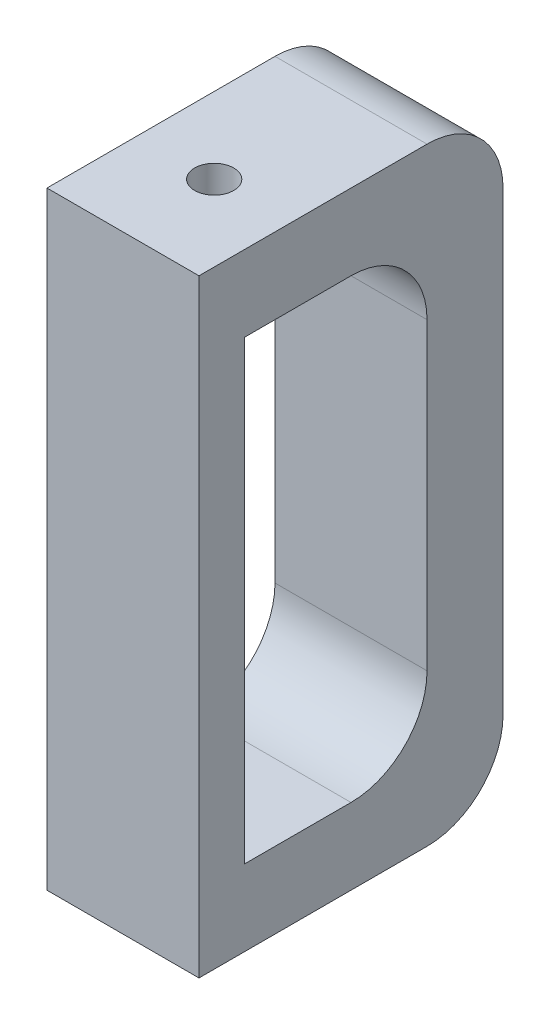
SolidWorks part; units mm, degrees
ref_plane "Front Plane" through (0, 0, 0) normal (0, 0, 1) x (1, 0, 0)
ref_plane "Top Plane" through (0, 0, 0) normal (0, 1, 0) x (1, 0, 0)
ref_plane "Right Plane" through (0, 0, 0) normal (1, 0, 0) x (0, 0, -1)
sketch "Sketch2" plane through (0, 0, 0) normal (0, 1, 0) x (1, 0, 0)
  line L0 (0, 2.159) -> (0, 0)
  line L1 (0, 0) -> (-3.937, 0)
  line L2 (-3.937, 0) -> (0, -5.7698)
  line L6 (6.35, 0) -> (6.35, 2.159)
  line L7 (6.35, 2.159) -> (0, 2.159)
  line L8 (6.35, 0) -> (10.287, 0)
  line L9 (10.287, 0) -> (6.35, -5.7698)
  line L10 (6.35, -5.7698) -> (0, -5.7698)
  dimension "D1" = 6.35
  dimension "D2" = 3.937
  dimension "D3" = 3.937
  dimension "D4" = 6.35
  dimension "D5" = 6.985
  dimension "D6" = 6.985
  dimension "D7" = 2.159
  dimension "D8" = 2.159
extrude "Boss-Extrude1" add sketch "Sketch2" against normal blind 101.6
sketch "Sketch3" plane through (0, 0, -2.159) normal (0, 0, -1) x (-1, 0, 0)
  line L0 (-6.35, 0) -> (0, 0) construction
  line L1 (-15.875, 0) -> (9.525, 0)
  line L2 (-15.875, 0) -> (-15.875, -101.6)
  line L3 (-15.875, -101.6) -> (9.525, -101.6)
  line L4 (9.525, 0) -> (9.525, -101.6)
  line L9 (-6.35, -101.6) -> (-6.35, 0) construction
  line L10 (-6.35, -101.6) -> (0, -101.6) construction
  dimension "D2" = 25.4
  dimension "D3" = 9.525
extrude "Boss-Extrude2" add sketch "Sketch3" along normal blind 50.8
sketch "Sketch5" plane through (15.875, 0, 0) normal (1, 0, 0) x (0, 0, -1)
  line L0 (2.159, 0) -> (40.259, 0)
  line L1 (52.959, -12.7) -> (52.959, -88.9)
  line L2 (40.259, -101.6) -> (2.159, -101.6)
  line L3 (2.159, -101.6) -> (2.159, 0)
  line L4 (9.779, -12.7) -> (9.779, -88.9)
  line L5 (9.779, -88.9) -> (27.559, -88.9)
  line L6 (40.259, -76.2) -> (40.259, -25.4)
  line L7 (27.559, -12.7) -> (9.779, -12.7)
  line L8 (40.259, 0) -> (52.959, 0)
  line L9 (52.959, 0) -> (52.959, -12.7)
  line L10 (40.259, -101.6) -> (52.959, -101.6)
  line L11 (52.959, -101.6) -> (52.959, -88.9)
  arc A0 (40.259, 0) -> (52.959, -12.7) centre (40.259, -12.7) cw
  arc A1 (52.959, -88.9) -> (40.259, -101.6) centre (40.259, -88.9) cw
  arc A2 (27.559, -88.9) -> (40.259, -76.2) centre (27.559, -76.2) ccw
  arc A3 (40.259, -25.4) -> (27.559, -12.7) centre (27.559, -25.4) ccw
  point P14 (52.959, 0)
  point P17 (52.959, -101.6)
  line M12 (2.159, -101.6) -> (52.959, -101.6)
  line M13 (52.959, -101.6) -> (52.959, 0)
  line M14 (52.959, 0) -> (2.159, 0)
  dimension "D5" = 12.7
  dimension "D1" = 7.62
  dimension "D2" = 12.7
  dimension "D3" = 12.7
  dimension "D4" = 12.7
extrude "Cut-Extrude2" cut sketch "Sketch5" against normal blind 25.4 contours A1 M13 M12 | A0 M14 M13 | L6 A3 L7 L4 L5 A2
sketch "Sketch6" plane through (0, 0, 0) normal (0, 1, 0) x (1, 0, 0)
  line L0 (6.35, 2.159) -> (15.875, 2.159) construction
  line L2 (-9.525, 40.259) -> (-9.525, 2.159) construction
  circle A0 centre (3.175, 17.399) radius 3.2639
  dimension "D1" = 6.5278
  dimension "D2" = 15.24
  dimension "D3" = 12.7
extrude "Cut-Extrude3" cut sketch "Sketch6" against normal up to surface (101.6 mm away) up to face at (3.175, -101.6, -6.4679)
sketch "Sketch7" plane through (0, 0, 0) normal (0, 1, 0) x (1, 0, 0)
  line L0 (-4.7625, 2.159) -> (-4.7625, -5.7698)
  line L1 (-9.525, 2.159) -> (0, 2.159) construction
  line L2 (-4.7625, -5.7698) -> (11.1125, -5.7698)
  line L3 (11.1125, -5.7698) -> (11.1125, 2.159)
  line L4 (6.35, 2.159) -> (15.875, 2.159) construction
  line L5 (11.1125, 2.159) -> (-4.7625, 2.159)
  line L6 (0, -5.7698) -> (6.35, -5.7698) construction
extrude "Cut-Extrude4" cut sketch "Sketch7" against normal through all both and the other way through all
